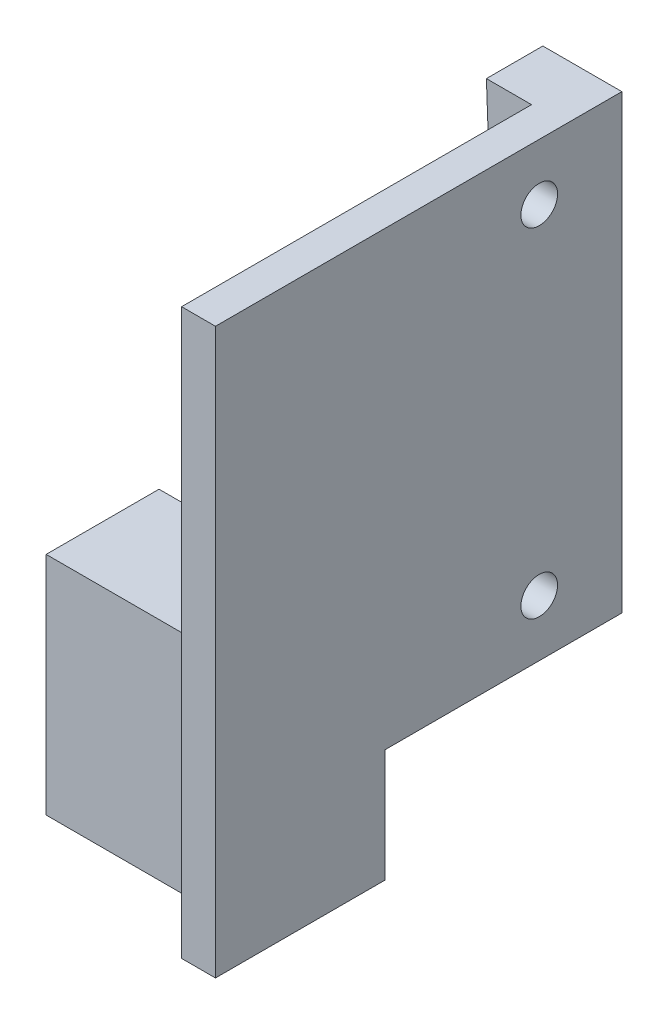
SolidWorks part; units mm, degrees
ref_plane "Plan de face" through (0, 0, 0) normal (0, 0, 1) x (1, 0, 0)
ref_plane "Plan de dessus" through (0, 0, 0) normal (0, 1, 0) x (1, 0, 0)
ref_plane "Plan de droite" through (0, 0, 0) normal (1, 0, 0) x (0, 0, -1)
sketch "Esquisse1" plane through (0, 0, 0) normal (0, 0, 1) x (1, 0, 0)
  line L1 (0, 0) -> (7, 0)
  line L2 (0, 0) -> (0, -40)
  line L3 (0, -40) -> (7, -40)
  line L4 (7, 0) -> (7, -40)
  dimension "D1" = 7
  dimension "D2" = 40
extrude "Boss.-Extru.1" add sketch "Esquisse1" along normal blind 5
sketch "Esquisse2" plane through (0, 0, 5) normal (0, 0, 1) x (1, 0, 0)
  line L0 (0, -40) -> (0, 0)
  line L1 (0, 0) -> (1.5, -40)
  line L2 (0, -40) -> (7, -40) construction
  line L3 (1.5, -40) -> (0, -40)
  dimension "D1" = 1.5
extrude "Enlèv. mat.-Extru.1" cut sketch "Esquisse2" against normal blind 5
sketch "Esquisse3" plane through (0, 0, 5) normal (0, 0, 1) x (1, 0, 0)
  line L0 (7, 0) -> (0, 0) construction
  line L1 (7, -40) -> (4, -40)
  line L2 (7, -40) -> (7, 0)
  line L3 (7, 0) -> (4, 0)
  line L4 (4, -40) -> (4, 0)
  dimension "D1" = 3
extrude "Boss.-Extru.2" add sketch "Esquisse3" along normal blind 6
sketch "Esquisse5" plane through (0, 0, 11) normal (0, 0, 1) x (1, 0, 0)
  line L0 (4, 0) -> (4, -40) construction
  line L1 (7, 0) -> (4, 0)
  line L2 (7, 0) -> (7, -10)
  line L3 (7, -10) -> (4, -10)
  line L4 (4, 0) -> (4, -10)
  dimension "D1" = 10
extrude "Boss.-Extru.3" add sketch "Esquisse5" along normal blind 25
sketch "Esquisse4" plane through (4, 0, 0) normal (-1, 0, 0) x (0, 0, 1)
  line L1 (36, 0) -> (5, 0) construction
  circle A0 centre (7.3208, -35) radius 1.625
  circle A1 centre (7.3208, -5) radius 1.625
  dimension "D1" = 3.25
  dimension "D2" = 3.25
  dimension "D3" = 30
  dimension "D4" = 5
extrude "Enlèv. mat.-Extru.2" cut sketch "Esquisse4" against normal through all
sketch "Esquisse9" plane through (0, 0, 11) normal (0, 0, 1) x (1, 0, 0)
  line L1 (7, -10) -> (4, -10)
  line L2 (7, -10) -> (7, -40)
  line L3 (7, -40) -> (4, -40)
  line L4 (4, -10) -> (4, -40)
extrude "Boss.-Extru.5" add sketch "Esquisse9" along normal blind 25
sketch "Esquisse10" plane through (0, -40, 0) normal (0, -1, 0) x (1, 0, 0)
  line L0 (7, 36) -> (7, 0) construction
  line L1 (4, 36) -> (7, 36)
  line L2 (4, 36) -> (4, 21)
  line L3 (4, 21) -> (7, 21)
  line L4 (7, 36) -> (7, 21)
  dimension "D1" = 15
extrude "Boss.-Extru.6" add sketch "Esquisse10" along normal blind 10
sketch "Esquisse11" plane through (4, 0, 0) normal (-1, 0, 0) x (0, 0, 1)
  line L0 (36, -50) -> (21, -50) construction
  line L1 (21, -30) -> (31, -30)
  line L2 (21, -30) -> (21, -50)
  line L3 (21, -50) -> (31, -50)
  line L4 (31, -30) -> (31, -50)
  dimension "D1" = 10
  dimension "D2" = 20
extrude "Boss.-Extru.7" add sketch "Esquisse11" along normal blind 17
sketch "Esquisse12" plane through (0, 0, 21) normal (0, 0, -1) x (-1, 0, 0)
  line L0 (-7, -50) -> (-7, -40) construction
  line L1 (13, -50) -> (-7, -50) construction
  circle A0 centre (5.3, -44.1) radius 2.6
  dimension "D1" = 5.2
  dimension "D2" = 12.3
  dimension "D3" = 5.9
extrude "Enlèv. mat.-Extru.3" cut sketch "Esquisse12" against normal blind 5
